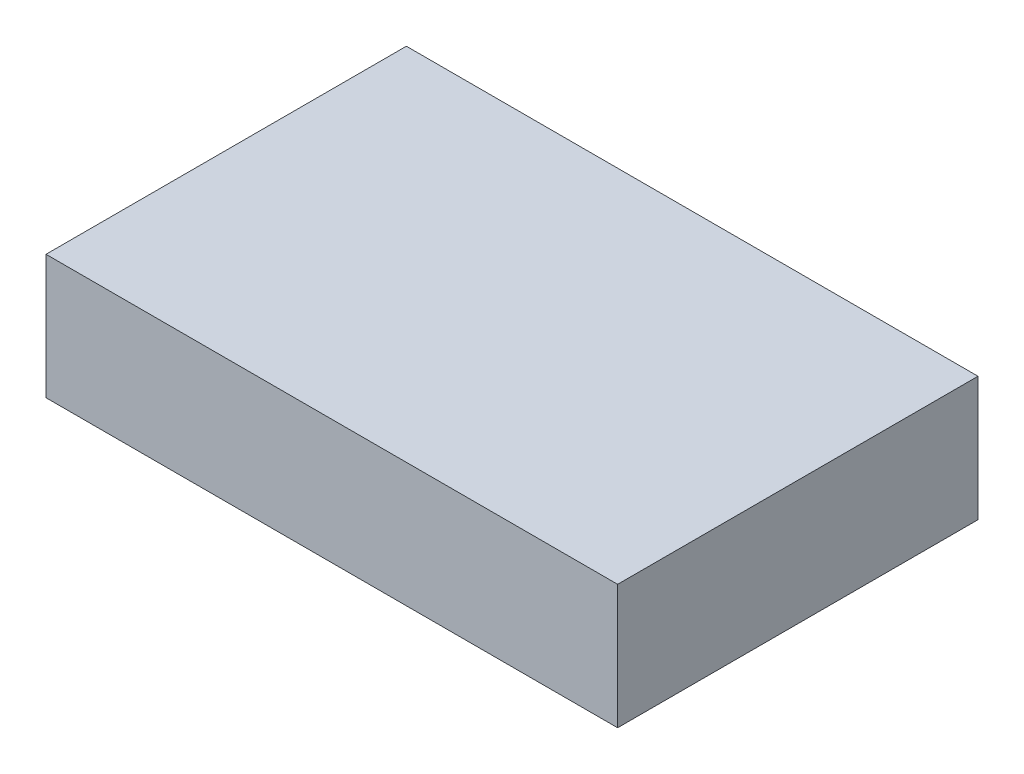
SolidWorks part; units mm, degrees
ref_plane "Front Plane" through (0, 0, 0) normal (0, 0, 1) x (1, 0, 0)
ref_plane "Top Plane" through (0, 0, 0) normal (0, 1, 0) x (1, 0, 0)
ref_plane "Right Plane" through (0, 0, 0) normal (1, 0, 0) x (0, 0, -1)
sketch "Sketch1" plane through (0, 0, 0) normal (0, 1, 0) x (1, 0, 0)
  line L1 (0, 0) -> (58.42, 0)
  line L2 (0, 0) -> (0, 36.83)
  line L3 (0, 36.83) -> (58.42, 36.83)
  line L4 (58.42, 0) -> (58.42, 36.83)
  dimension "D1" = 36.83
  dimension "D2" = 58.42
extrude "Boss-Extrude1" add sketch "Sketch1" along normal blind 12.7
